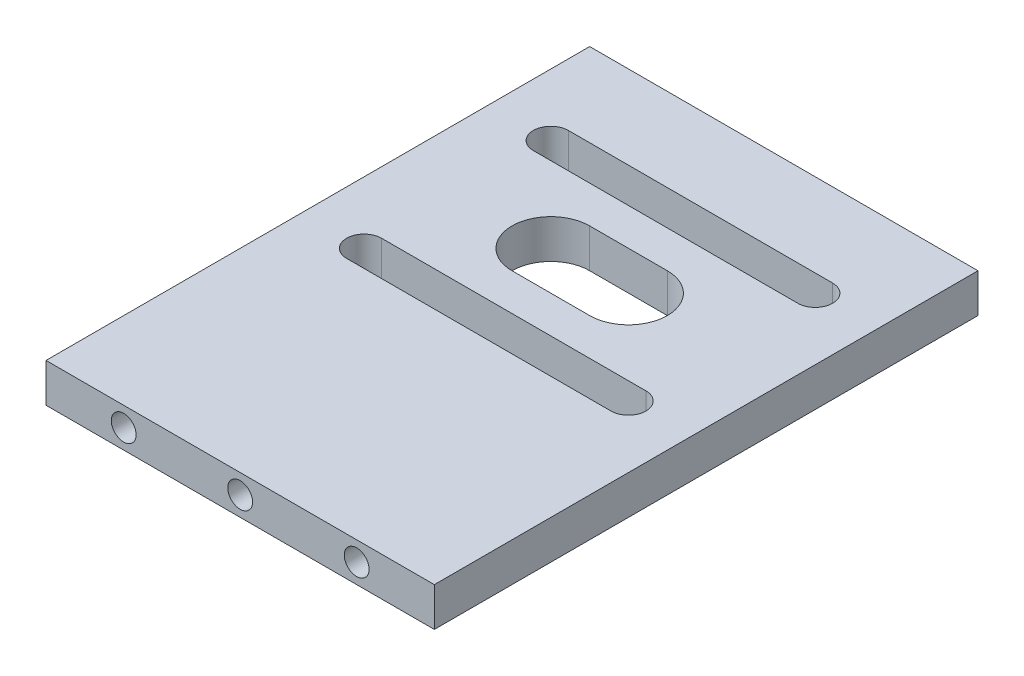
SolidWorks part; units mm, degrees
ref_plane "Front Plane" through (0, 0, 0) normal (0, 0, 1) x (1, 0, 0)
ref_plane "Top Plane" through (0, 0, 0) normal (0, 1, 0) x (1, 0, 0)
ref_plane "Right Plane" through (0, 0, 0) normal (1, 0, 0) x (0, 0, -1)
sketch "Sketch1" plane through (0, 0, 0) normal (0, 1, 0) x (1, 0, 0)
  line L0 (15.4249, 43.2744) -> (15.4249, -26.7256)
  line L1 (-34.5751, 43.2744) -> (15.4249, 43.2744)
  line L2 (-34.5751, 43.2744) -> (-34.5751, -26.7256)
  line L3 (-34.5751, -26.7256) -> (15.4249, -26.7256)
  line L5 (-26.5959, 30.2952) -> (7.4457, 30.2952) construction
  line L6 (-26.5959, 32.5452) -> (7.4457, 32.5452)
  line L7 (-26.5959, 28.0452) -> (7.4457, 28.0452)
  line L8 (-19.5751, 33.2744) -> (10.4249, 33.2744) construction
  line L9 (-19.5751, 33.2744) -> (-19.5751, 3.2744) construction
  line L10 (-19.5751, 3.2744) -> (10.4249, 3.2744) construction
  line L11 (10.4249, 33.2744) -> (10.4249, 3.2744) construction
  line L12 (-19.5751, 33.2744) -> (10.4249, 3.2744) construction
  line L13 (-19.5751, 3.2744) -> (10.4249, 33.2744) construction
  line L14 (-14.5751, 18.2744) -> (-4.5751, 18.2744) construction
  line L15 (-14.5751, 18.2744) -> (-4.5751, 18.2744) construction
  line L16 (-14.5751, 23.2744) -> (-4.5751, 23.2744)
  line L17 (-14.5751, 13.2744) -> (-4.5751, 13.2744)
  line L18 (-26.5959, 6.2536) -> (7.4457, 6.2536) construction
  line L19 (-26.5959, 4.0036) -> (7.4457, 4.0036)
  line L20 (-26.5959, 8.5036) -> (7.4457, 8.5036)
  circle A0 centre (-4.5751, 18.2744) radius 17 construction
  circle A1 centre (-16.5959, 30.2952) radius 2.25 construction
  arc A2 (-26.5959, 32.5452) -> (-26.5959, 28.0452) centre (-26.5959, 30.2952) ccw
  arc A3 (7.4457, 28.0452) -> (7.4457, 32.5452) centre (7.4457, 30.2952) ccw
  circle A4 centre (-4.5751, 18.2744) radius 4 construction
  arc A5 (-14.5751, 23.2744) -> (-14.5751, 13.2744) centre (-14.5751, 18.2744) ccw
  arc A6 (-4.5751, 13.2744) -> (-4.5751, 23.2744) centre (-4.5751, 18.2744) ccw
  arc A7 (-26.5959, 4.0036) -> (-26.5959, 8.5036) centre (-26.5959, 6.2536) cw
  arc A8 (7.4457, 8.5036) -> (7.4457, 4.0036) centre (7.4457, 6.2536) cw
  point P0 (0, 0)
  point P6 (9.6957, 30.2952)
  point P7 (15.4249, 30.2952)
  point P8 (-4.5751, 18.2744)
  point P9 (-4.5751, 18.2744)
  point P18 (7.4457, 30.2952)
  point P19 (-26.5959, 30.2952)
  point P22 (-9.5751, 30.2952)
  point P28 (-14.5751, 18.2744)
  point P30 (-9.5751, 18.2744)
  point P37 (-9.5751, 6.2536)
  point P42 (-28.8459, 30.2952)
  dimension "D6" = 10
  dimension "D7" = 2.25
  dimension "D8" = 10
  dimension "D9" = 5
  dimension "D12" = 34
  dimension "D1" = 70
  dimension "D2" = 25
  dimension "D3" = 30
  dimension "D4" = 30
  dimension "D5" = 30
  dimension "D10" = 20
  dimension "D11" = 17
extrude "Boss-Extrude1" add sketch "Sketch1" along normal blind 5
sketch "Sketch2" plane through (0, 0, 26.7256) normal (0, 0, 1) x (1, 0, 0)
  line L0 (-34.5751, 2.5) -> (15.4249, 2.5) construction
  line L1 (-34.5751, 5) -> (-34.5751, 0) construction
  line L2 (15.4249, 5) -> (15.4249, 0) construction
  line L3 (-9.5751, 5) -> (-9.5751, 0) construction
  line L4 (-34.5751, 5) -> (15.4249, 5) construction
  line L5 (-34.5751, 0) -> (15.4249, 0) construction
  circle A0 centre (-9.5751, 2.5) radius 1.6
  circle A1 centre (-24.5751, 2.5) radius 1.6
  circle A2 centre (5.4249, 2.5) radius 1.6
  point P14 (-24.5751, 2.5)
  dimension "D1" = 10
extrude "Cut-Extrude1" cut sketch "Sketch2" against normal blind 10
